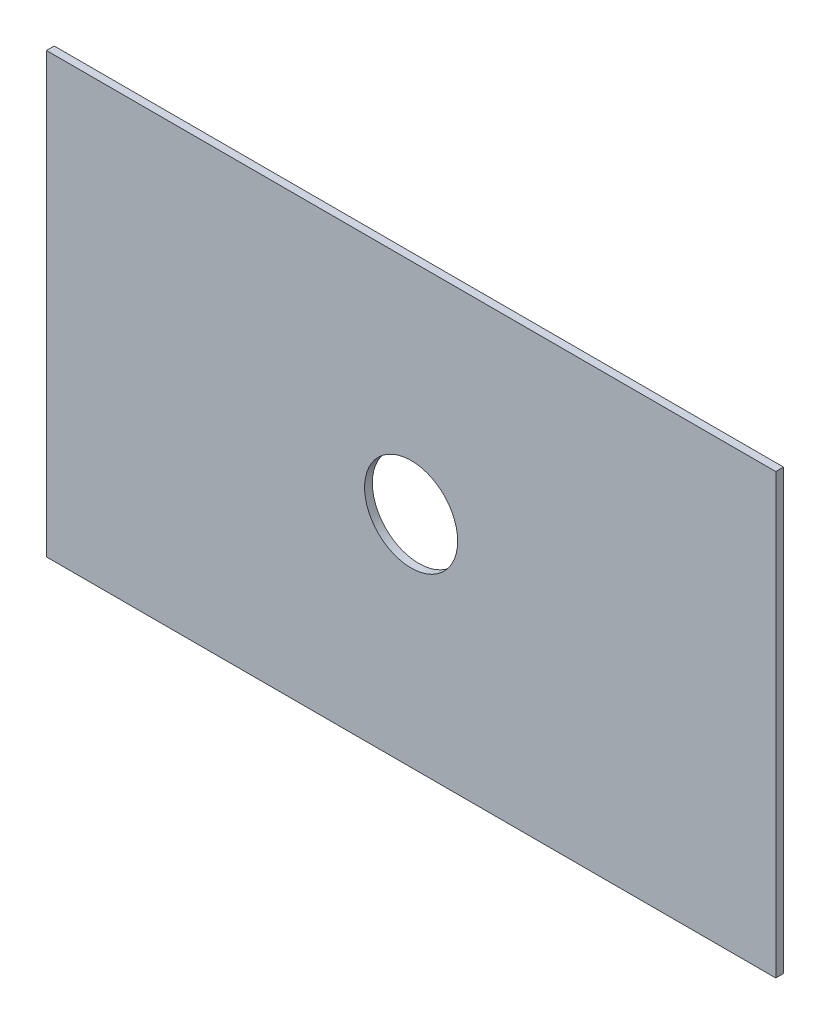
SolidWorks part; units mm, degrees
material "Gomma siliconata"
ref_plane "Piano frontale" through (0, 0, 0) normal (0, 0, 1) x (1, 0, 0)
ref_plane "Piano superiore" through (0, 0, 0) normal (0, 1, 0) x (1, 0, 0)
ref_plane "Piano destro" through (0, 0, 0) normal (1, 0, 0) x (0, 0, -1)
sketch "Schizzo2" plane through (0, 0, 0) normal (0, 0, 1) x (1, 0, 0)
  line L0 (23.5001, -14.1332) -> (25.0001, -14.1332) construction
  line L1 (-23.5001, -14.1332) -> (23.5001, -14.1332)
  line L2 (-23.5001, -14.1332) -> (-23.5001, 14.1332)
  line L3 (-23.5001, 14.1332) -> (23.5001, 14.1332)
  line L4 (23.5001, -14.1332) -> (23.5001, 14.1332)
  line L5 (-23.5001, -14.1332) -> (23.5001, 14.1332) construction
  line L6 (-23.5001, 14.1332) -> (23.5001, -14.1332) construction
  line L7 (25.0001, -15.6332) -> (25.0001, 16.4373) construction
  line L8 (23.5001, -14.1332) -> (23.5001, -15.6332) construction
  line L9 (-24.9999, -15.6332) -> (25.0001, -15.6332) construction
  point P0 (0, 0)
  dimension "D1" = 1.5
extrude "Estrusione-Estrusione1" add sketch "Schizzo2" along normal blind 0.5
sketch "Schizzo3" plane through (0, 0, 0.5) normal (0, 0, 1) x (1, 0, 0)
  circle A0 centre (0, 0) radius 3
  dimension "D1" = 6
extrude "Taglio-Estrusione1" cut sketch "Schizzo3" against normal blind 1
